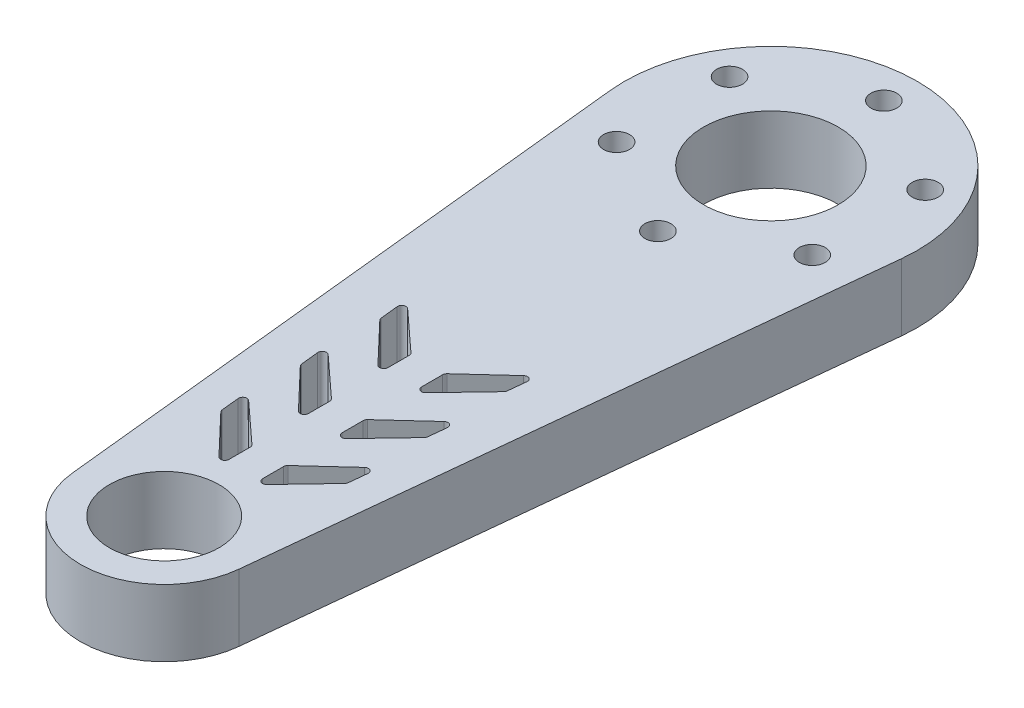
SolidWorks part; units mm, degrees
material "Thornel Mat VMA"
ref_plane "前视基准面" through (0, 0, 0) normal (0, 0, 1) x (1, 0, 0)
ref_plane "上视基准面" through (0, 0, 0) normal (0, 1, 0) x (1, 0, 0)
ref_plane "右视基准面" through (0, 0, 0) normal (1, 0, 0) x (0, 0, -1)
ref_plane "基准面4" through (0, 4, 0) normal (0, 1, 0) x (1, 0, 0)
sketch "草图1" plane through (0, 4, 0) normal (0, 1, 0) x (1, 0, 0)
  line L0 (-17.4061, -1.8103) -> (-9.9463, -73.5345)
  line L1 (9.9463, -73.5345) -> (17.4061, -1.8103)
  arc A0 (-9.9463, -73.5345) -> (9.9463, -73.5345) centre (0, -72.5) ccw
  arc A1 (17.4061, -1.8103) -> (-17.4061, -1.8103) centre (0, 0) ccw
extrude "凸台-拉伸1" add sketch "草图1" against normal blind 8
sketch "草图2" plane through (0, 4, 0) normal (0, 1, 0) x (-1, 0, 0)
  line L0 (2, 43.7505) -> (2, 41)
  line L1 (2, 41) -> (6.9232, 36.4832)
  line L2 (7.7585, 36.9034) -> (7.5188, 39.2084)
  line L3 (7.5188, 39.2084) -> (2.862, 44.0954)
  arc A0 (2.862, 44.0954) -> (2, 43.7505) centre (2.5, 43.7505) ccw
  arc A1 (6.9232, 36.4832) -> (7.7585, 36.9034) centre (7.2612, 36.8517) ccw
extrude "切除-拉伸1" cut sketch "草图2" against normal through all
sketch "草图3" plane through (0, 4, 0) normal (0, 1, 0) x (-1, 0, 0)
  line L0 (-6.9232, 36.4832) -> (-2, 41)
  line L1 (-2, 41) -> (-2, 43.7505)
  line L2 (-2.862, 44.0954) -> (-7.5188, 39.2084)
  line L3 (-7.5188, 39.2084) -> (-7.7585, 36.9034)
  arc A0 (-2, 43.7505) -> (-2.862, 44.0954) centre (-2.5, 43.7505) ccw
  arc A1 (-7.7585, 36.9034) -> (-6.9232, 36.4832) centre (-7.2612, 36.8517) ccw
extrude "切除-拉伸2" cut sketch "草图3" against normal through all
sketch "草图4" plane through (0, 4, 0) normal (0, 1, 0) x (-1, 0, 0)
  line L0 (2, 53.2505) -> (2, 50.5)
  line L1 (2, 50.5) -> (6.9232, 45.9832)
  line L2 (7.7585, 46.4034) -> (7.5188, 48.7084)
  line L3 (7.5188, 48.7084) -> (2.862, 53.5954)
  arc A0 (2.862, 53.5954) -> (2, 53.2505) centre (2.5, 53.2505) ccw
  arc A1 (6.9232, 45.9832) -> (7.7585, 46.4034) centre (7.2612, 46.3517) ccw
extrude "切除-拉伸3" cut sketch "草图4" against normal through all
sketch "草图5" plane through (0, 4, 0) normal (0, 1, 0) x (-1, 0, 0)
  line L0 (-6.9232, 45.9832) -> (-2, 50.5)
  line L1 (-2, 50.5) -> (-2, 53.2505)
  line L2 (-2.862, 53.5954) -> (-7.5188, 48.7084)
  line L3 (-7.5188, 48.7084) -> (-7.7585, 46.4034)
  arc A0 (-2, 53.2505) -> (-2.862, 53.5954) centre (-2.5, 53.2505) ccw
  arc A1 (-7.7585, 46.4034) -> (-6.9232, 45.9832) centre (-7.2612, 46.3517) ccw
extrude "切除-拉伸4" cut sketch "草图5" against normal through all
sketch "草图6" plane through (0, 4, 0) normal (0, 1, 0) x (-1, 0, 0)
  line L0 (2, 62.7505) -> (2, 60)
  line L1 (2, 60) -> (6.9232, 55.4832)
  line L2 (7.7585, 55.9034) -> (7.5188, 58.2084)
  line L3 (7.5188, 58.2084) -> (2.862, 63.0954)
  arc A0 (2.862, 63.0954) -> (2, 62.7505) centre (2.5, 62.7505) ccw
  arc A1 (6.9232, 55.4832) -> (7.7585, 55.9034) centre (7.2612, 55.8517) ccw
extrude "切除-拉伸5" cut sketch "草图6" against normal through all
sketch "草图7" plane through (0, -4, 0) normal (0, -1, 0) x (1, 0, 0)
  line L0 (2, 62.7505) -> (2, 60)
  line L1 (2, 60) -> (6.9232, 55.4832)
  line L2 (7.7585, 55.9034) -> (7.5188, 58.2084)
  line L3 (7.5188, 58.2084) -> (2.862, 63.0954)
  arc A0 (6.9232, 55.4832) -> (7.7585, 55.9034) centre (7.2612, 55.8517) ccw
  arc A1 (2.862, 63.0954) -> (2, 62.7505) centre (2.5, 62.7505) ccw
extrude "切除-拉伸6" cut sketch "草图7" against normal through all
hole_wizard "Ø16.0 (16) 直径孔1" positions "草图12" profile "草图11" hole size "Ø16.0" standard "ANSI Metric"
sketch "草图12" plane through (0, -4, 0) normal (0, -1, 0) x (-1, 0, 0)
  point P0 (0, 0)
sketch "草图11" plane through (0, -4, 0) normal (1, 0, 0) x (0, 0, -1)
  line L0 (0, 0) -> (0, 8)
  line L1 (0, 8) -> (8.05, 8)
  line L2 (8.05, 8) -> (8.05, 0)
  line L5 (8.05, 0) -> (0, 0)
  line L11 (0, -6.35) -> (0, 107.95) construction
  dimension "通孔孔直径" = 16.1
  dimension "通孔孔深度" = 8
hole_wizard "Ø13.0 (13) 直径孔1" positions "草图14" profile "草图13" hole size "Ø13.0" standard "ANSI Metric"
sketch "草图14" plane through (0, 4, 0) normal (0, 1, 0) x (1, 0, 0)
  point P0 (0, -72.5)
sketch "草图13" plane through (0, 4, 72.5) normal (1, 0, 0) x (0, 0, 1)
  line L0 (0, 0) -> (0, 8)
  line L1 (0, 8) -> (6.55, 8)
  line L2 (6.55, 8) -> (6.55, 0)
  line L5 (6.55, 0) -> (0, 0)
  line L11 (0, -6.35) -> (0, 107.95) construction
  dimension "通孔孔直径" = 13.1
  dimension "通孔孔深度" = 8
hole_wizard "M2.5 六角头机械螺钉的柱形沉头孔1" positions "草图16" profile "草图15" counterbore size "M2.5" standard "ANSI Metric"
sketch "草图16" plane through (0, -4, 0) normal (0, -1, 0) x (-1, 0, 0)
  point P0 (11.6913, -6.75)
  point P1 (11.6913, 6.75)
  point P2 (0, 13.5)
  point P3 (-11.6913, 6.75)
  point P4 (-11.6913, -6.75)
  point P5 (0, -13.5)
sketch "草图15" plane through (-11.6913, -4, 6.75) normal (1, 0, 0) x (0, 0, -1)
  line L0 (0, 0) -> (0, 8)
  line L1 (0, 8) -> (1.55, 8)
  line L3 (1.55, 8) -> (1.55, 3)
  line L4 (1.55, 3) -> (2.8, 3)
  line L5 (2.8, 3) -> (2.8, 0)
  line L7 (2.8, 0) -> (0, 0)
  line L11 (0, -6.35) -> (0, 107.95) construction
  dimension "通孔孔直径" = 3.1
  dimension "通孔孔深度" = 8
  dimension "柱形沉头孔直径" = 5.6
  dimension "柱形沉头孔深度" = 3
fillet "圆角1" radius 0.5 12 edges at (-7.5188, 0, 48.7084) (-7.5188, 0, 58.2084) (7.5188, 0, 48.7084) (-2, 0, 60) (2, 0, 41) (2, 0, 60) (-2, 0, 50.5) (-7.5188, 0, 39.2084) (2, 0, 50.5) (-2, 0, 41) (7.5188, 0, 39.2084) (7.5188, 0, 58.2084)
